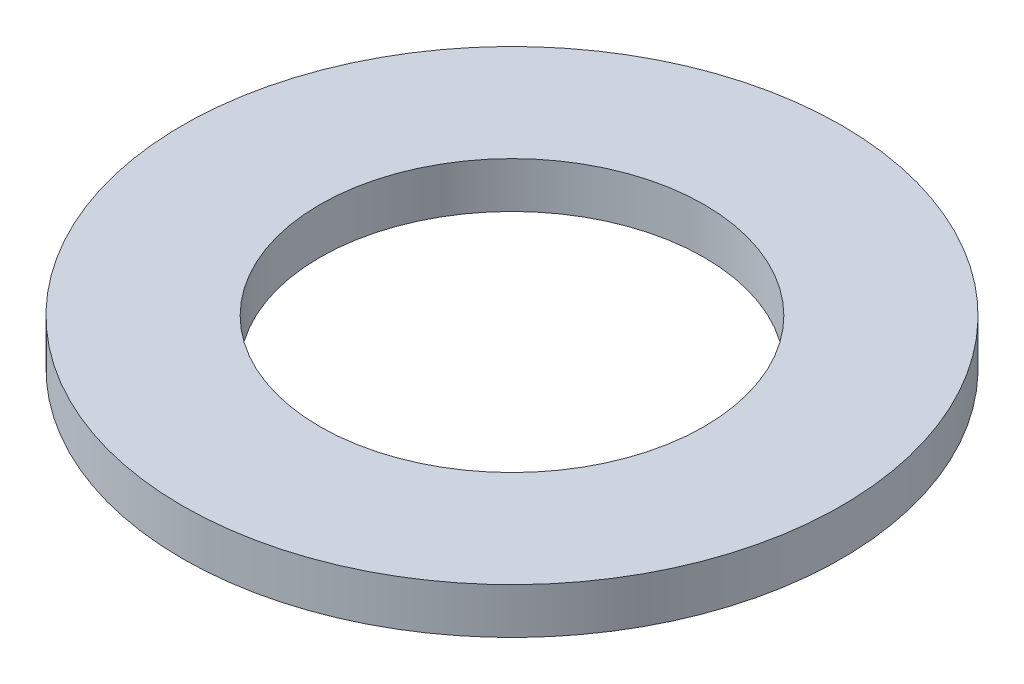
SolidWorks part; units mm, degrees
material "1060-O (SS)"
ref_plane "Ebene vorne" through (0, 0, 0) normal (0, 0, 1) x (1, 0, 0)
ref_plane "Ebene oben" through (0, 0, 0) normal (0, 1, 0) x (1, 0, 0)
ref_plane "Ebene rechts" through (0, 0, 0) normal (1, 0, 0) x (0, 0, -1)
sketch "Sketch1" plane through (0, 0, 0) normal (0, 0, 1) x (1, 0, 0)
  line L0 (0, 0) -> (0, 2.4219) construction
  line L1 (-4.2, 0) -> (-7.2, 0)
  line L2 (-4.2, 0) -> (-4.2, 1)
  line L3 (-4.2, 1) -> (-7.2, 1)
  line L4 (-7.2, 0) -> (-7.2, 1)
  dimension "D1" = 1
  dimension "D2" = 3
  dimension "D3" = 4.2
revolve "Revolve1" add sketch "Sketch1" angle 360 about L0
